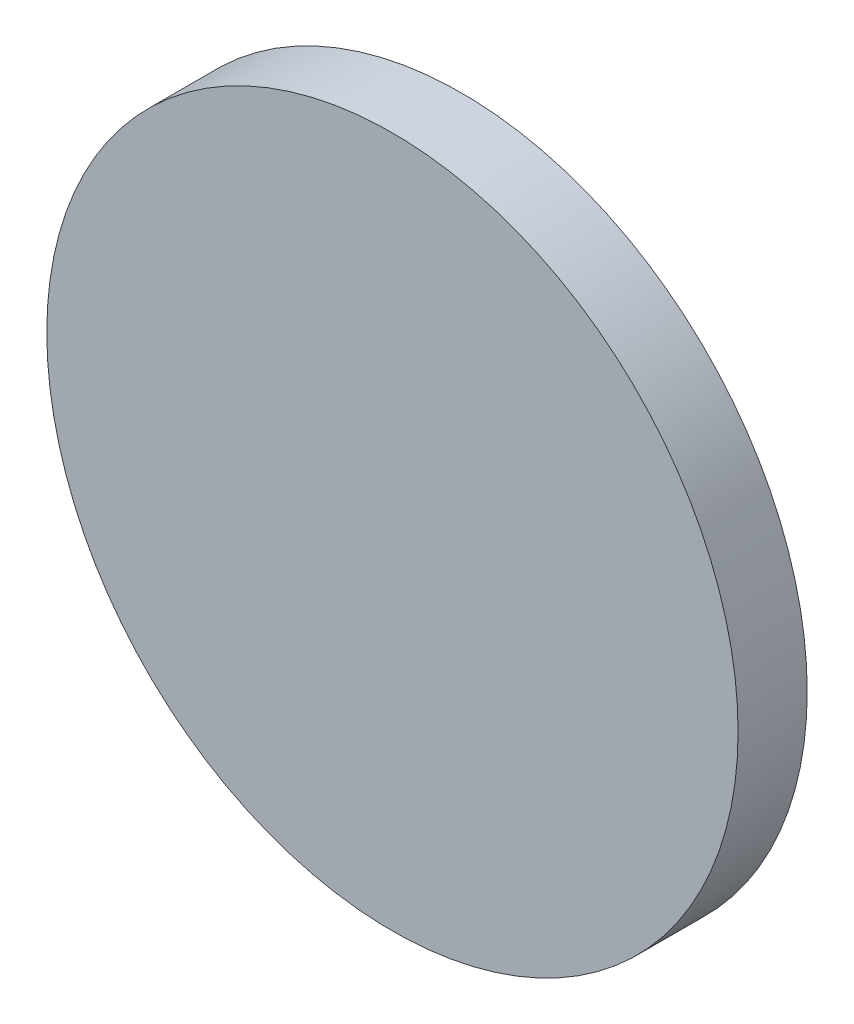
SolidWorks part; units mm, degrees
ref_plane "Front Plane" through (0, 0, 0) normal (0, 0, 1) x (1, 0, 0)
ref_plane "Top Plane" through (0, 0, 0) normal (0, 1, 0) x (1, 0, 0)
ref_plane "Right Plane" through (0, 0, 0) normal (1, 0, 0) x (0, 0, -1)
sketch "Sketch1" plane through (0, 0, 0) normal (0, 0, 1) x (1, 0, 0)
  circle A0 centre (-85, 68) radius 15 construction
  circle A1 centre (-85, 68) radius 15
extrude "Boss-Extrude1" add sketch "Sketch1" along normal blind 3
